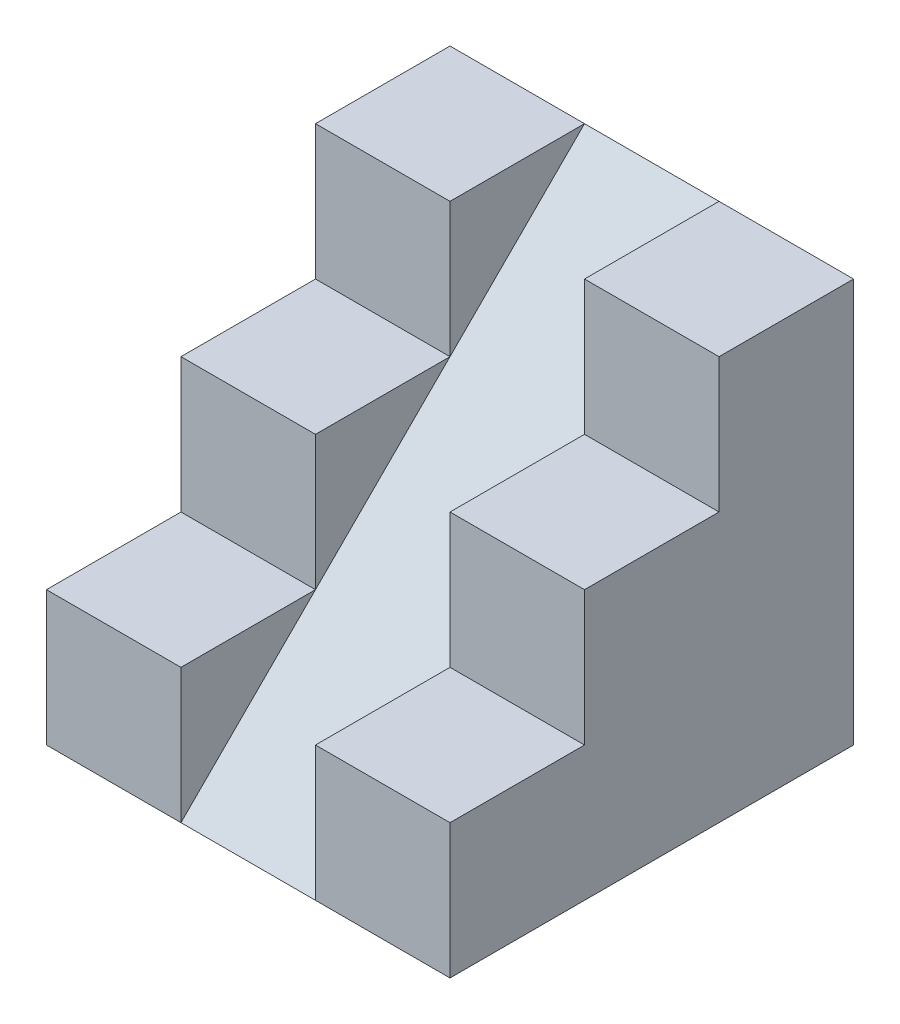
SolidWorks part; units mm, degrees
ref_plane "Alzado" through (0, 0, 0) normal (0, 0, 1) x (1, 0, 0)
ref_plane "Planta" through (0, 0, 0) normal (0, 1, 0) x (1, 0, 0)
ref_plane "Vista lateral" through (0, 0, 0) normal (1, 0, 0) x (0, 0, -1)
sketch "Croquis4" plane through (0, 0, 0) normal (0, 0, 1) x (1, 0, 0)
  line L0 (0, 0) -> (60, 0)
  line L1 (0, 0) -> (0, 60)
  line L2 (0, 60) -> (60, 60)
  line L3 (60, 60) -> (60, 0)
  dimension "D1" = 60
  dimension "D2" = 60
extrude "Saliente-Extruir1" add sketch "Croquis4" along normal blind 60
sketch "Croquis10" plane through (60, 0, 0) normal (1, 0, 0) x (0, 0, -1)
  line L0 (0, 20) -> (0, 40)
  line L1 (0, 0) -> (-20, 0)
  line L2 (0, 0) -> (0, 20)
  line L3 (0, 20) -> (-20, 20)
  line L4 (-20, 0) -> (-20, 20)
  line L5 (0, 20) -> (-20, 20)
  line L6 (-20, 20) -> (-20, 40)
  line L7 (0, 40) -> (-20, 40)
  line L8 (0, 40) -> (0, 60)
  line L9 (0, 40) -> (-20, 40)
  line L10 (-20, 40) -> (-20, 60)
  line L11 (0, 60) -> (-20, 60)
  line L12 (-20, 40) -> (-20, 60)
  line L13 (-20, 60) -> (-40, 60)
  line L14 (-40, 40) -> (-40, 60)
  line L15 (-20, 40) -> (-40, 40)
  line L16 (-20, 20) -> (-20, 40)
  line L17 (-20, 40) -> (-40, 40)
  line L18 (-40, 20) -> (-40, 40)
  line L19 (-20, 20) -> (-40, 20)
  line L20 (-20, 0) -> (-20, 20)
  line L21 (-20, 0) -> (-40, 0)
  line L22 (-40, 0) -> (-40, 20)
  line L23 (-20, 20) -> (-40, 20)
  line L24 (-40, 40) -> (-40, 60)
  line L25 (-40, 60) -> (-60, 60)
  line L26 (-60, 40) -> (-60, 60)
  line L27 (-40, 40) -> (-60, 40)
  line L28 (-40, 20) -> (-40, 40)
  line L29 (-40, 40) -> (-60, 40)
  line L30 (-60, 20) -> (-60, 40)
  line L31 (-40, 20) -> (-60, 20)
  line L32 (-40, 0) -> (-40, 20)
  line L33 (-40, 0) -> (-60, 0)
  line L34 (-60, 0) -> (-60, 20)
  line L35 (-40, 20) -> (-60, 20)
  line M2 (0, 60) -> (-60, 60)
  line M3 (-60, 60) -> (-60, 0)
  dimension "D1" = 20
  dimension "D2" = 20
  dimension "D3" = 3
  dimension "D4" = 3
extrude "Cortar-Extruir6" cut sketch "Croquis10" against normal blind 60 contours L15 L10 L14 M2 | L27 L14 M2 M3 | L31 L18 L27 M3
sketch "Croquis11" plane through (0, 60, 0) normal (0, 1, 0) x (1, 0, 0)
  line L0 (0, -20) -> (60, -20) construction
  line L1 (0, 0) -> (20, 0)
  line L2 (0, 0) -> (0, -20)
  line L3 (0, -20) -> (20, -20)
  line L4 (20, 0) -> (20, -20)
  line L5 (20, 0) -> (20, -20)
  line L6 (20, 0) -> (40, 0)
  line L7 (40, 0) -> (40, -20)
  line L8 (20, -20) -> (40, -20)
  line L9 (40, 0) -> (40, -20)
  line L10 (40, 0) -> (60, 0)
  line L11 (60, 0) -> (60, -20)
  line L12 (40, -20) -> (60, -20)
  dimension "D1" = 20
  dimension "D2" = 3
extrude "Cortar-Extruir7" cut sketch "Croquis11" against normal blind 20 contours L5 L8 L7 L6
sketch "Croquis12" plane through (20, 0, 0) normal (1, 0, 0) x (0, 0, -1)
  line L0 (0, 60) -> (0, 40)
  line L1 (0, 40) -> (-20, 40)
  line L2 (-20, 40) -> (0, 60)
extrude "Saliente-Extruir2" add sketch "Croquis12" along normal blind 20
sketch "Croquis13" plane through (0, 40, 0) normal (0, 1, 0) x (1, 0, 0)
  line L0 (0, -40) -> (60, -40) construction
  line L1 (0, -20) -> (20, -20)
  line L2 (0, -20) -> (0, -40)
  line L3 (0, -40) -> (20, -40)
  line L4 (20, -20) -> (20, -40)
  line L5 (20, -20) -> (20, -40)
  line L6 (20, -20) -> (40, -20)
  line L7 (40, -20) -> (40, -40)
  line L8 (20, -40) -> (40, -40)
  dimension "D1" = 2
extrude "Cortar-Extruir8" cut sketch "Croquis13" against normal blind 20 contours L5 L8 L7 L6
sketch "Croquis14" plane through (20, 0, 0) normal (1, 0, 0) x (0, 0, -1)
  line L0 (-20, 40) -> (-40, 20)
  line L1 (-40, 20) -> (-20, 20)
  line L2 (-20, 20) -> (-20, 40)
  line L3 (0, 60) -> (-60, 0)
  line L4 (-60, 0) -> (-40, 0)
  line L5 (-60, 0) -> (0, 0) construction
  line L6 (-40, 0) -> (-40, 20)
  line L7 (-20, 40) -> (0, 40)
  line L8 (0, 0) -> (0, 60) construction
  line L9 (0, 40) -> (0, 60)
  line M3 (-40, 20) -> (-20, 20)
  line M4 (-20, 20) -> (-20, 40)
extrude "Saliente-Extruir3" add sketch "Croquis14" along normal blind 20 contours L0 M4 M3
sketch "Croquis16" plane through (60, 0, 0) normal (1, 0, 0) x (0, 0, -1)
  line L0 (-40, 20) -> (-60, 0)
  line L1 (-60, 0) -> (-60, 20)
  line L2 (-60, 20) -> (-40, 20)
extrude "Cortar-Extruir9" cut sketch "Croquis16" along normal blind 20 from offset 40 offset against normal yes
